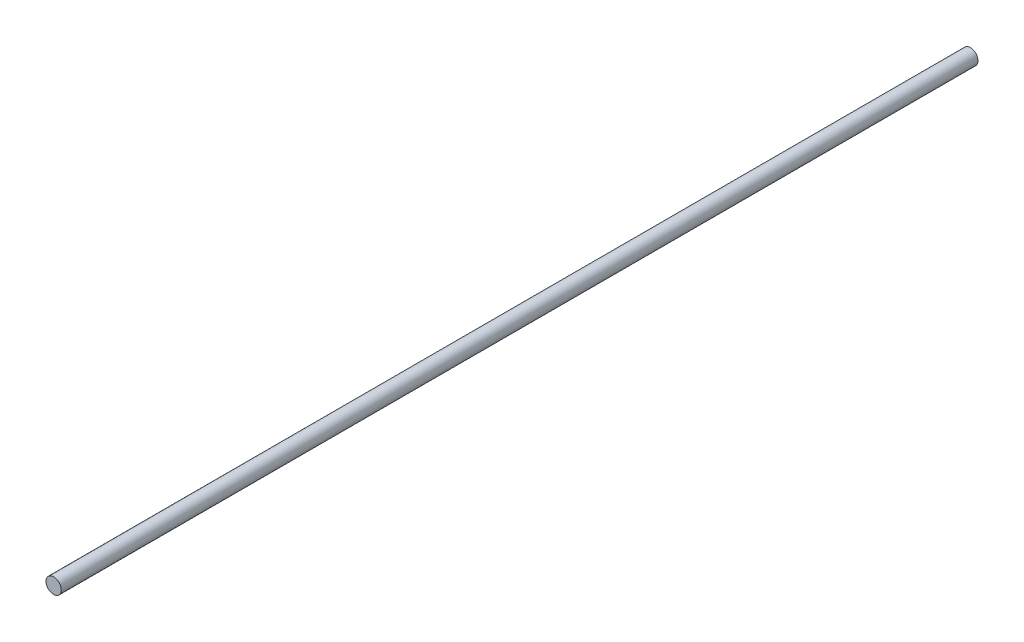
SolidWorks part; units mm, degrees
material "1023 Carbon Steel Sheet (SS)"
ref_plane "Front Plane" through (0, 0, 0) normal (0, 0, 1) x (1, 0, 0)
ref_plane "Top Plane" through (0, 0, 0) normal (0, 1, 0) x (1, 0, 0)
ref_plane "Right Plane" through (0, 0, 0) normal (1, 0, 0) x (0, 0, -1)
sketch "Sketch1" plane through (0, 0, 0) normal (0, 0, 1) x (1, 0, 0)
  circle A0 centre (0, 0) radius 6.35
  dimension "D1" = 12.7
extrude "Boss-Extrude1" add sketch "Sketch1" along normal mid plane 762
